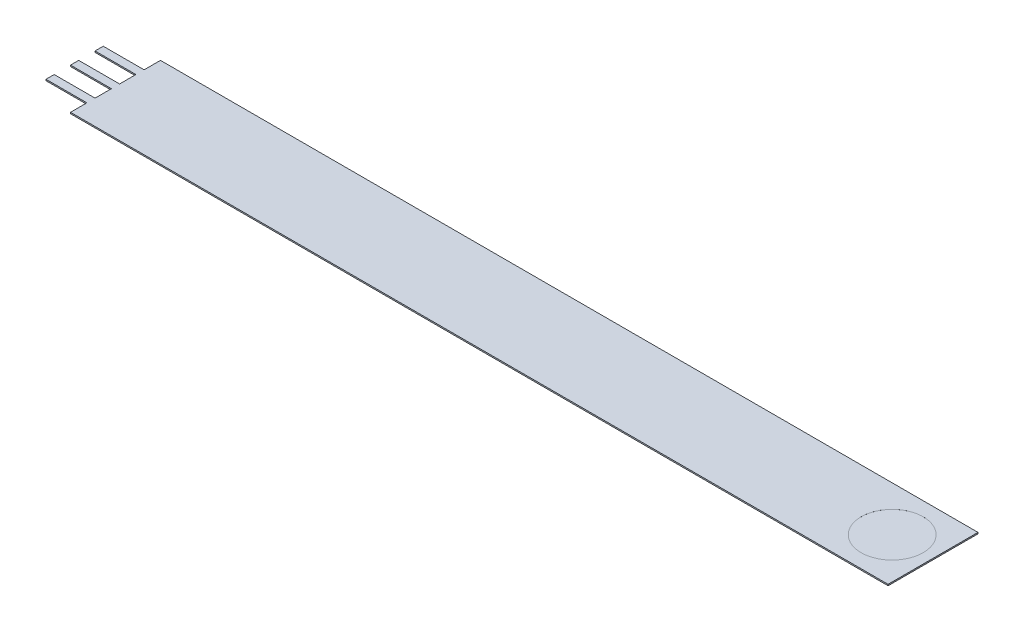
SolidWorks part; units mm, degrees
ref_plane "Front Plane" through (0, 0, 0) normal (0, 0, 1) x (1, 0, 0)
ref_plane "Top Plane" through (0, 0, 0) normal (0, 1, 0) x (1, 0, 0)
ref_plane "Right Plane" through (0, 0, 0) normal (1, 0, 0) x (0, 0, -1)
sketch "Sketch1" plane through (0, 0, 0) normal (0, 1, 0) x (1, 0, 0)
  line L0 (-118.11, -6.985) -> (-118.11, 6.985) construction
  line L1 (-76.2, -6.985) -> (-76.2, 6.985) construction
  line L2 (-120.65, -0.635) -> (-127, -0.635)
  line L3 (-120.65, 6.985) -> (6.35, 6.985)
  line L4 (-120.65, 6.985) -> (-120.65, 4.445)
  line L5 (-120.65, -6.985) -> (6.35, -6.985)
  line L6 (6.35, 6.985) -> (6.35, -6.985)
  line L7 (-120.65, 0.635) -> (-120.65, 3.175) construction
  line L9 (-120.65, 0.635) -> (-127, 0.635)
  line L10 (-127, -0.635) -> (-127, 0.635)
  line L11 (-120.65, 3.175) -> (-127, 3.175)
  line L13 (-120.65, 4.445) -> (-127, 4.445)
  line L14 (-127, 3.175) -> (-127, 4.445)
  line L15 (-120.65, -3.175) -> (-127, -3.175)
  line L17 (-120.65, -4.445) -> (-127, -4.445)
  line L18 (-127, -3.175) -> (-127, -4.445)
  line L19 (-120.65, 3.175) -> (-120.65, 0.635)
  line L20 (-120.65, 4.445) -> (-120.65, 6.985) construction
  line L21 (-120.65, -0.635) -> (-120.65, -3.175)
  line L22 (-120.65, -4.445) -> (-120.65, -6.985)
  circle A0 centre (0, 0) radius 4.826 construction
  point P3 (6.35, 0)
  point P7 (-76.2, 0)
  point P24 (-127, 0)
  point P27 (-118.11, 0)
  dimension "D1" = 9.652
  dimension "D2" = 6.35
  dimension "D3" = 13.97
  dimension "D4" = 127
  dimension "D5" = 6.35
  dimension "D6" = 1.27
  dimension "D7" = 2.54
  dimension "D8" = 2.54
  dimension "D9" = 13.97
  dimension "D10" = 6.985
  dimension "D11" = 2.54
  dimension "D12" = 76.2
  dimension "D13" = 6.985
extrude "Boss-Extrude1" add sketch "Sketch1" along normal blind 0.2032
sketch "Sketch2" plane through (0, 0.2032, 0) normal (0, 1, 0) x (1, 0, 0)
  circle A0 centre (0, 0) radius 4.826
extrude "Cut-Extrude1" cut sketch "Sketch2" against normal blind 0.0025
